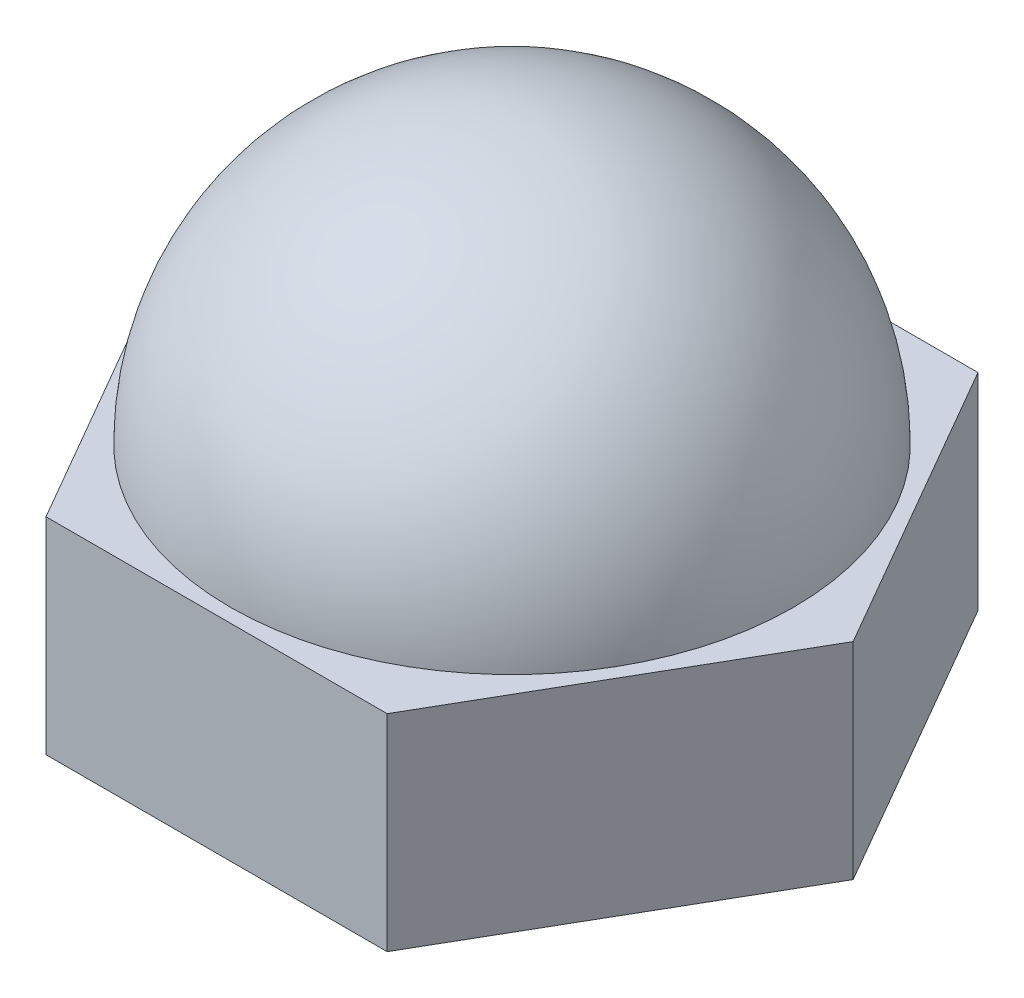
SolidWorks part; units mm, degrees
ref_plane "Front Plane" through (0, 0, 0) normal (0, 0, 1) x (1, 0, 0)
ref_plane "Top Plane" through (0, 0, 0) normal (0, 1, 0) x (1, 0, 0)
ref_plane "Right Plane" through (0, 0, 0) normal (1, 0, 0) x (0, 0, -1)
sketch "Sketch1" plane through (0, 0, 0) normal (0, 1, 0) x (1, 0, 0)
  line L1 (4.9652, 0) -> (2.4826, 4.3)
  line L2 (2.4826, 4.3) -> (-2.4826, 4.3)
  line L3 (-2.4826, 4.3) -> (-4.9652, 0)
  line L4 (-4.9652, 0) -> (-2.4826, -4.3)
  line L5 (-2.4826, -4.3) -> (2.4826, -4.3)
  line L6 (2.4826, -4.3) -> (4.9652, 0)
  circle A0 centre (0, 0) radius 4.3 construction
  circle A1 centre (0, 0) radius 4
extrude "Boss-Extrude1" add sketch "Sketch1" along normal blind 3
sketch "Sketch2" plane through (0, 0, 0) normal (0, 0, 1) x (1, 0, 0)
  line L0 (-2.4826, 3) -> (2.4826, 3) construction
  line L1 (0, -3.905) -> (0, 3.905) construction
  line L2 (2.4826, 3) -> (4.9652, 3) construction
  line L3 (4.1, 3) -> (0, 3)
  arc A0 (0, 7.1) -> (4.1, 3) centre (0, 3) cw
ref_axis "Axis1" through (0, 7.455, 0) along (0, -1, 0)
revolve "Revolve-Thin1" add sketch "Sketch2" angle 360 about axis through (0, 7.455, 0) along (0, -1, 0)
